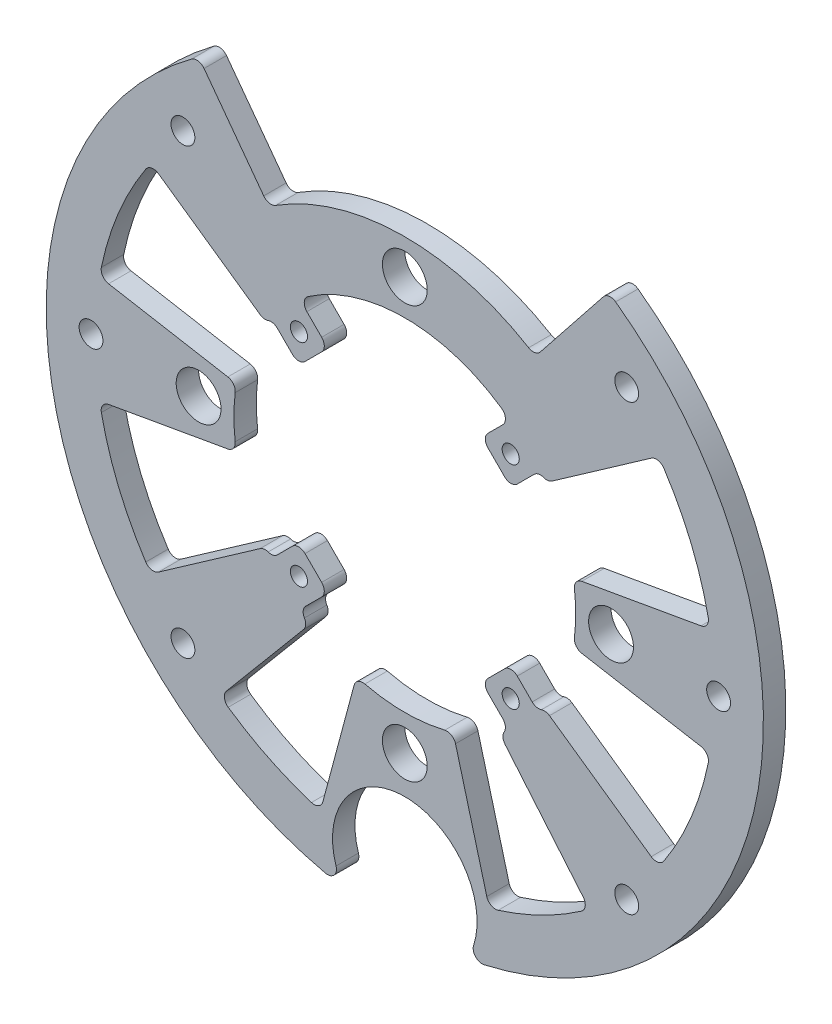
SolidWorks part; units mm, degrees
ref_plane "Front Plane" through (0, 0, 0) normal (0, 0, 1) x (1, 0, 0)
ref_plane "Top Plane" through (0, 0, 0) normal (0, 1, 0) x (1, 0, 0)
ref_plane "Right Plane" through (0, 0, 0) normal (1, 0, 0) x (0, 0, -1)
ref_plane "Plane1" through (0, 0, 6.35) normal (0, 0, 1) x (1, 0, 0)
sketch "Sketch1" plane through (0, 0, 6.35) normal (0, 0, 1) x (1, 0, 0)
  line L0 (57.7446, 83.595) -> (36.9784, 57.4547)
  line L1 (-38.5448, 56.4158) -> (-58.3635, 83.164)
  arc A0 (-58.3635, 83.164) -> (-22.4668, -99.0848) centre (0, 0) ccw
  arc A1 (-22.4668, -99.0848) -> (-19.488, -95.8273) centre (-21.9052, -96.6077) ccw
  arc A2 (-19.488, -95.8273) -> (19.488, -95.8273) centre (0, -89.535) ccw
  arc A3 (19.488, -95.8273) -> (22.4668, -99.0848) centre (21.9052, -96.6077) ccw
  arc A4 (22.4668, -99.0848) -> (57.7446, 83.595) centre (0, 0) ccw
  arc A5 (36.9784, 57.4547) -> (-38.5448, 56.4158) centre (0, 0) ccw
extrude "Boss-Extrude1" add sketch "Sketch1" against normal blind 6.35
sketch "Sketch2" plane through (0, 0, 0) normal (0, 0, -1) x (-1, 0, 0)
  line L0 (86.468, -15.2466) -> (47.7, -8.4108)
  line L1 (47.7, 8.4108) -> (86.468, 15.2466)
  line L2 (71.9231, 50.3611) -> (40.9959, 28.7056)
  line L3 (36.0857, 27.7803) -> (30.0672, 21.7618)
  line L4 (30.0672, 21.7618) -> (21.7618, 30.0672)
  line L5 (21.7618, 30.0672) -> (29.8439, 38.1494)
  line L6 (-29.8439, 38.1494) -> (-21.7618, 30.0672)
  line L7 (-21.7618, 30.0672) -> (-30.0672, 21.7618)
  line L8 (-30.0672, 21.7618) -> (-36.639, 28.3336)
  line L9 (-41.7051, 29.2022) -> (-71.9231, 50.3611)
  line L10 (-86.468, 15.2466) -> (-47.7, 8.4108)
  line L11 (-47.7, -8.4108) -> (-86.468, -15.2466)
  line L12 (-71.9231, -50.3611) -> (-40.9959, -28.7056)
  line L13 (-36.0857, -27.7803) -> (-30.0672, -21.7618)
  line L14 (-30.0672, -21.7618) -> (-21.7618, -30.0672)
  line L15 (-21.7618, -30.0672) -> (-27.7507, -36.0561)
  line L16 (-28.3955, -42.047) -> (-52.2951, -70.5294)
  line L17 (-23.9004, -84.4864) -> (-13.71, -46.455)
  line L18 (13.7096, -46.4551) -> (23.9004, -84.4864)
  line L19 (52.2951, -70.5294) -> (28.6795, -42.3834)
  line L20 (28.0543, -36.3597) -> (21.7618, -30.0672)
  line L21 (21.7618, -30.0672) -> (30.0672, -21.7618)
  line L22 (30.0672, -21.7618) -> (36.0857, -27.7803)
  line L23 (40.9959, -28.7056) -> (71.9231, -50.3611)
  arc A0 (71.9231, -50.3611) -> (86.468, -15.2466) centre (0, 0) ccw
  arc A1 (47.7, -8.4108) -> (47.7, 8.4108) centre (0, 0) ccw
  arc A2 (86.468, 15.2466) -> (71.9231, 50.3611) centre (0, 0) ccw
  arc A3 (40.9959, 28.7056) -> (38.7104, 28.3852) centre (39.539, 30.7863) cw
  arc A4 (38.7104, 28.3852) -> (36.0857, 27.7803) centre (37.8817, 25.9842) ccw
  arc A5 (29.8439, 38.1494) -> (-29.8439, 38.1494) centre (0, 0) ccw
  arc A6 (-36.639, 28.3336) -> (-39.3416, 28.9102) centre (-38.435, 26.5375) ccw
  arc A7 (-39.3416, 28.9102) -> (-41.7051, 29.2022) centre (-40.2482, 31.2829) cw
  arc A8 (-71.9231, 50.3611) -> (-86.468, 15.2466) centre (0, 0) ccw
  arc A9 (-47.7, 8.4108) -> (-47.7, -8.4108) centre (0, 0) ccw
  arc A10 (-86.468, -15.2466) -> (-71.9231, -50.3611) centre (0, 0) ccw
  arc A11 (-40.9959, -28.7056) -> (-38.7104, -28.3852) centre (-39.539, -30.7863) cw
  arc A12 (-38.7104, -28.3852) -> (-36.0857, -27.7803) centre (-37.8817, -25.9842) ccw
  arc A13 (-27.7507, -36.0561) -> (-28.1479, -39.1332) centre (-25.9547, -37.8522) ccw
  arc A14 (-28.1479, -39.1332) -> (-28.3955, -42.047) centre (-30.3412, -40.4143) cw
  arc A15 (-52.2951, -70.5294) -> (-23.9004, -84.4864) centre (0, 0) ccw
  arc A16 (-13.71, -46.455) -> (13.7096, -46.4551) centre (0, 0) ccw
  arc A17 (23.9004, -84.4864) -> (52.2951, -70.5294) centre (0, 0) ccw
  arc A18 (28.6795, -42.3834) -> (28.4418, -39.4533) centre (30.6253, -40.7508) cw
  arc A19 (28.4418, -39.4533) -> (28.0543, -36.3597) centre (26.2582, -38.1557) ccw
  arc A20 (36.0857, -27.7803) -> (38.7104, -28.3852) centre (37.8817, -25.9842) ccw
  arc A21 (38.7104, -28.3852) -> (40.9959, -28.7056) centre (39.539, -30.7863) cw
extrude "Cut-Extrude1" cut sketch "Sketch2" against normal through all
ref_plane "Plane2" through (0, -89.535, 0) normal (0, -1, 0) x (1, 0, 0)
sketch "Sketch3" plane through (0, -89.535, 0) normal (0, -1, 0) x (1, 0, 0)
  line L0 (20.4787, 6.35) -> (0, 6.35)
  line L1 (0, 6.35) -> (0, 0)
  line L2 (0, 0) -> (20.4787, 0)
  line L3 (20.4787, 0) -> (20.4787, 6.35)
  line L4 (0, 6.35) -> (0, 0) construction
revolve "Cut-Revolve1" cut sketch "Sketch3" angle 360 about L4
hole_wizard "Hole1" positions "Sketch5" profile "Sketch4" legacy
sketch "Sketch5" plane through (0, 0, 6.35) normal (0, 0, 1) x (1, 0, 0)
  point P0 (29.9999, 29.9999)
sketch "Sketch4" plane through (29.9999, 29.9999, 6.35) normal (1, 0, 0) x (0, -1, 0)
  line L0 (0, 0) -> (0, 6.35)
  line L1 (0, 6.35) -> (2.4265, 6.35)
  line L2 (2.4265, 6.35) -> (2.4265, 0)
  line L3 (2.4265, 0) -> (0, 0)
  line L4 (0, 110) -> (0, -10) construction
  dimension "Diameter" = 4.853
  dimension "Depth" = 6.35
hole_wizard "Hole2" positions "Sketch7" profile "Sketch6" legacy
sketch "Sketch7" plane through (0, 0, 6.35) normal (0, 0, 1) x (1, 0, 0)
  point P0 (-29.9999, 29.9999)
sketch "Sketch6" plane through (-29.9999, 29.9999, 6.35) normal (1, 0, 0) x (0, -1, 0)
  line L0 (0, 0) -> (0, 6.35)
  line L1 (0, 6.35) -> (2.4265, 6.35)
  line L2 (2.4265, 6.35) -> (2.4265, 0)
  line L3 (2.4265, 0) -> (0, 0)
  line L4 (0, 110) -> (0, -10) construction
  dimension "Diameter" = 4.853
  dimension "Depth" = 6.35
hole_wizard "Hole3" positions "Sketch9" profile "Sketch8" legacy end condition through all
sketch "Sketch9" plane through (0, 0, 6.35) normal (0, 0, 1) x (1, 0, 0)
  point P0 (-29.9999, -29.9999)
sketch "Sketch8" plane through (-29.9999, -29.9999, 6.35) normal (1, 0, 0) x (0, -1, 0)
  line L0 (0, 0) -> (0, 6.35)
  line L1 (0, 6.35) -> (2.4265, 6.35)
  line L2 (2.4265, 6.35) -> (2.4265, 0)
  line L3 (2.4265, 0) -> (0, 0)
  line L4 (0, 110) -> (0, -10) construction
  dimension "Diameter" = 4.853
  dimension "Depth" = 6.35
hole_wizard "Hole4" positions "Sketch11" profile "Sketch10" legacy
sketch "Sketch11" plane through (0, 0, 6.35) normal (0, 0, 1) x (1, 0, 0)
  point P0 (29.9999, -29.9999)
sketch "Sketch10" plane through (29.9999, -29.9999, 6.35) normal (1, 0, 0) x (0, -1, 0)
  line L0 (0, 0) -> (0, 6.35)
  line L1 (0, 6.35) -> (2.4265, 6.35)
  line L2 (2.4265, 6.35) -> (2.4265, 0)
  line L3 (2.4265, 0) -> (0, 0)
  line L4 (0, 110) -> (0, -10) construction
  dimension "Diameter" = 4.853
  dimension "Depth" = 6.35
hole_wizard "Hole5" positions "Sketch13" profile "Sketch12" legacy
sketch "Sketch13" plane through (0, 0, 6.35) normal (0, 0, 1) x (1, 0, 0)
  point P0 (0, 58.42)
sketch "Sketch12" plane through (0, 58.42, 6.35) normal (1, 0, 0) x (0, -1, 0)
  line L0 (0, 0) -> (0, 6.35)
  line L1 (0, 6.35) -> (6.35, 6.35)
  line L2 (6.35, 6.35) -> (6.35, 0)
  line L3 (6.35, 0) -> (0, 0)
  line L4 (0, 110) -> (0, -10) construction
  dimension "Diameter" = 12.7
  dimension "Depth" = 6.35
hole_wizard "Hole6" positions "Sketch15" profile "Sketch14" legacy
sketch "Sketch15" plane through (0, 0, 6.35) normal (0, 0, 1) x (1, 0, 0)
  point P0 (58.42, 0)
sketch "Sketch14" plane through (58.42, 0, 6.35) normal (1, 0, 0) x (0, -1, 0)
  line L0 (0, 0) -> (0, 6.35)
  line L1 (0, 6.35) -> (6.35, 6.35)
  line L2 (6.35, 6.35) -> (6.35, 0)
  line L3 (6.35, 0) -> (0, 0)
  line L4 (0, 110) -> (0, -10) construction
  dimension "Diameter" = 12.7
  dimension "Depth" = 6.35
hole_wizard "Hole7" positions "Sketch17" profile "Sketch16" legacy
sketch "Sketch17" plane through (0, 0, 6.35) normal (0, 0, 1) x (1, 0, 0)
  point P0 (-58.42, 0)
sketch "Sketch16" plane through (-58.42, 0, 6.35) normal (1, 0, 0) x (0, -1, 0)
  line L0 (0, 0) -> (0, 6.35)
  line L1 (0, 6.35) -> (6.35, 6.35)
  line L2 (6.35, 6.35) -> (6.35, 0)
  line L3 (6.35, 0) -> (0, 0)
  line L4 (0, 110) -> (0, -10) construction
  dimension "Diameter" = 12.7
  dimension "Depth" = 6.35
hole_wizard "Hole8" positions "Sketch19" profile "Sketch18" legacy
sketch "Sketch19" plane through (0, 0, 6.35) normal (0, 0, 1) x (1, 0, 0)
  point P0 (0, -58.42)
sketch "Sketch18" plane through (0, -58.42, 6.35) normal (1, 0, 0) x (0, -1, 0)
  line L0 (0, 0) -> (0, 6.35)
  line L1 (0, 6.35) -> (6.35, 6.35)
  line L2 (6.35, 6.35) -> (6.35, 0)
  line L3 (6.35, 0) -> (0, 0)
  line L4 (0, 110) -> (0, -10) construction
  dimension "Diameter" = 12.7
  dimension "Depth" = 6.35
hole_wizard "Hole9" positions "Sketch21" profile "Sketch20" legacy
sketch "Sketch21" plane through (0, 0, 6.35) normal (0, 0, 1) x (1, 0, 0)
  point P0 (62.8618, -62.8618)
sketch "Sketch20" plane through (62.8618, -62.8618, 6.35) normal (1, 0, 0) x (0, -1, 0)
  line L0 (0, 0) -> (0, 8.3798)
  line L1 (0, 8.3798) -> (3.3782, 6.35)
  line L2 (3.3782, 6.35) -> (3.3782, 0)
  line L4 (3.3782, 0) -> (0, 0)
  line L6 (0, 8.3798) -> (-3.3782, 6.35) construction
  line L7 (0, -4.2442) -> (0, 117.3081) construction
  dimension "Diameter" = 6.7564
  dimension "Depth" = 6.35
  dimension "Drill Angle" = 118
hole_wizard "Hole10" positions "Sketch23" profile "Sketch22" legacy end condition through all
sketch "Sketch23" plane through (0, 0, 6.35) normal (0, 0, 1) x (1, 0, 0)
  point P0 (88.9, 0)
sketch "Sketch22" plane through (88.9, 0, 6.35) normal (1, 0, 0) x (0, -1, 0)
  line L0 (0, 0) -> (0, 8.3798)
  line L1 (0, 8.3798) -> (3.3782, 6.35)
  line L2 (3.3782, 6.35) -> (3.3782, 0)
  line L4 (3.3782, 0) -> (0, 0)
  line L6 (0, 8.3798) -> (-3.3782, 6.35) construction
  line L7 (0, -4.2442) -> (0, 117.3081) construction
  dimension "Diameter" = 6.7564
  dimension "Depth" = 6.35
  dimension "Drill Angle" = 118
hole_wizard "Hole11" positions "Sketch25" profile "Sketch24" legacy
sketch "Sketch25" plane through (0, 0, 6.35) normal (0, 0, 1) x (1, 0, 0)
  point P0 (62.8618, 62.8618)
sketch "Sketch24" plane through (62.8618, 62.8618, 6.35) normal (1, 0, 0) x (0, -1, 0)
  line L0 (0, 0) -> (0, 8.3798)
  line L1 (0, 8.3798) -> (3.3782, 6.35)
  line L2 (3.3782, 6.35) -> (3.3782, 0)
  line L4 (3.3782, 0) -> (0, 0)
  line L6 (0, 8.3798) -> (-3.3782, 6.35) construction
  line L7 (0, -4.2442) -> (0, 117.3081) construction
  dimension "Diameter" = 6.7564
  dimension "Depth" = 6.35
  dimension "Drill Angle" = 118
hole_wizard "Hole12" positions "Sketch27" profile "Sketch26" legacy
sketch "Sketch27" plane through (0, 0, 6.35) normal (0, 0, 1) x (1, 0, 0)
  point P0 (-62.8618, 62.8618)
sketch "Sketch26" plane through (-62.8618, 62.8618, 6.35) normal (1, 0, 0) x (0, -1, 0)
  line L0 (0, 0) -> (0, 8.3798)
  line L1 (0, 8.3798) -> (3.3782, 6.35)
  line L2 (3.3782, 6.35) -> (3.3782, 0)
  line L4 (3.3782, 0) -> (0, 0)
  line L6 (0, 8.3798) -> (-3.3782, 6.35) construction
  line L7 (0, -4.2442) -> (0, 117.3081) construction
  dimension "Diameter" = 6.7564
  dimension "Depth" = 6.35
  dimension "Drill Angle" = 118
hole_wizard "Hole13" positions "Sketch29" profile "Sketch28" legacy
sketch "Sketch29" plane through (0, 0, 6.35) normal (0, 0, 1) x (1, 0, 0)
  point P0 (-88.9, 0)
sketch "Sketch28" plane through (-88.9, 0, 6.35) normal (1, 0, 0) x (0, -1, 0)
  line L0 (0, 0) -> (0, 8.3798)
  line L1 (0, 8.3798) -> (3.3782, 6.35)
  line L2 (3.3782, 6.35) -> (3.3782, 0)
  line L4 (3.3782, 0) -> (0, 0)
  line L6 (0, 8.3798) -> (-3.3782, 6.35) construction
  line L7 (0, -4.2442) -> (0, 117.3081) construction
  dimension "Diameter" = 6.7564
  dimension "Depth" = 6.35
  dimension "Drill Angle" = 118
hole_wizard "Hole14" positions "Sketch31" profile "Sketch30" legacy end condition through all
sketch "Sketch31" plane through (0, 0, 6.35) normal (0, 0, 1) x (1, 0, 0)
  point P0 (-62.8618, -62.8618)
sketch "Sketch30" plane through (-62.8618, -62.8618, 6.35) normal (1, 0, 0) x (0, -1, 0)
  line L0 (0, 0) -> (0, 8.3798)
  line L1 (0, 8.3798) -> (3.3782, 6.35)
  line L2 (3.3782, 6.35) -> (3.3782, 0)
  line L4 (3.3782, 0) -> (0, 0)
  line L6 (0, 8.3798) -> (-3.3782, 6.35) construction
  line L7 (0, -4.2442) -> (0, 117.3081) construction
  dimension "Diameter" = 6.7564
  dimension "Depth" = 6.35
  dimension "Drill Angle" = 118
fillet "Fillet1" radius 2.54 1 edges at (-86.468, 15.2466, 3.175)
fillet "Fillet2" radius 2.54 1 edges at (-52.2951, -70.5294, 3.175)
fillet "Fillet3" radius 2.54 1 edges at (-38.5448, 56.4158, 3.175)
fillet "Fillet4" radius 2.54 1 edges at (-23.9004, -84.4864, 3.175)
fillet "Fillet5" radius 2.54 1 edges at (29.8439, 38.1494, 3.175)
fillet "Fillet6" radius 2.54 1 edges at (71.9231, -50.3611, 3.175)
fillet "Fillet7" radius 2.54 1 edges at (-71.9231, -50.3611, 3.175)
fillet "Fillet8" radius 2.54 1 edges at (-13.7096, -46.4551, 3.175)
fillet "Fillet9" radius 2.54 1 edges at (86.468, -15.2466, 3.175)
fillet "Fillet10" radius 2.54 1 edges at (-47.7, 8.4108, 3.175)
fillet "Fillet11" radius 2.54 1 edges at (-71.9231, 50.3611, 3.175)
fillet "Fillet12" radius 2.54 1 edges at (57.7446, 83.595, 3.175)
fillet "Fillet13" radius 2.54 1 edges at (52.2951, -70.5294, 3.175)
fillet "Fillet14" radius 2.54 1 edges at (47.7, 8.4108, 3.175)
fillet "Fillet15" radius 2.54 1 edges at (23.9004, -84.4864, 3.175)
fillet "Fillet16" radius 2.54 1 edges at (-86.468, -15.2466, 3.175)
fillet "Fillet17" radius 2.54 1 edges at (13.71, -46.455, 3.175)
fillet "Fillet18" radius 2.54 1 edges at (71.9231, 50.3611, 3.175)
fillet "Fillet19" radius 2.54 1 edges at (86.468, 15.2466, 3.175)
fillet "Fillet20" radius 2.54 1 edges at (47.7, -8.4108, 3.175)
fillet "Fillet21" radius 2.54 1 edges at (21.7618, 30.0672, 3.175)
fillet "Fillet22" radius 2.54 1 edges at (30.0672, -21.7618, 3.175)
fillet "Fillet23" radius 2.54 1 edges at (21.7618, -30.0672, 3.175)
fillet "Fillet24" radius 2.54 1 edges at (-21.7618, 30.0672, 3.175)
fillet "Fillet25" radius 2.54 1 edges at (-47.7, -8.4108, 3.175)
fillet "Fillet26" radius 2.54 1 edges at (-21.7618, -30.0672, 3.175)
fillet "Fillet27" radius 2.54 1 edges at (30.0672, 21.7618, 3.175)
fillet "Fillet28" radius 2.54 1 edges at (36.9784, 57.4547, 3.175)
fillet "Fillet29" radius 2.54 1 edges at (-30.0672, 21.7618, 3.175)
fillet "Fillet30" radius 2.54 1 edges at (-30.0672, -21.7618, 3.175)
fillet "Fillet31" radius 2.54 1 edges at (-29.8439, 38.1494, 3.175)
fillet "Fillet32" radius 2.54 1 edges at (-58.3635, 83.164, 3.175)
